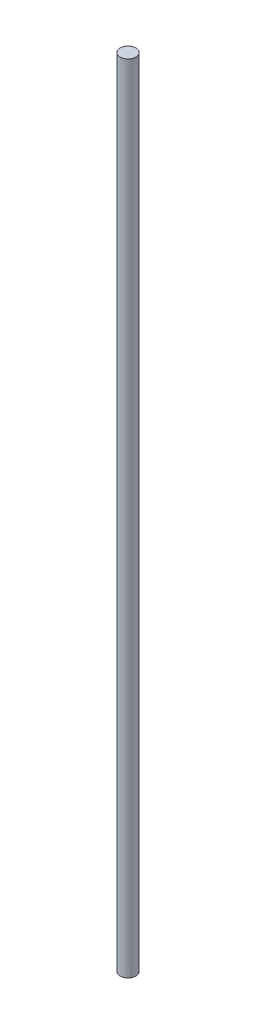
SolidWorks part; units mm, degrees
ref_plane "Front Plane" through (0, 0, 0) normal (0, 0, 1) x (1, 0, 0)
ref_plane "Top Plane" through (0, 0, 0) normal (0, 1, 0) x (1, 0, 0)
ref_plane "Right Plane" through (0, 0, 0) normal (1, 0, 0) x (0, 0, -1)
sketch "Sketch1" plane through (0, 0, 0) normal (0, 1, 0) x (1, 0, 0)
  circle A0 centre (0, 0) radius 1.5
  dimension "D1" = 3
extrude "Boss-Extrude1" add sketch "Sketch1" along normal blind 150
